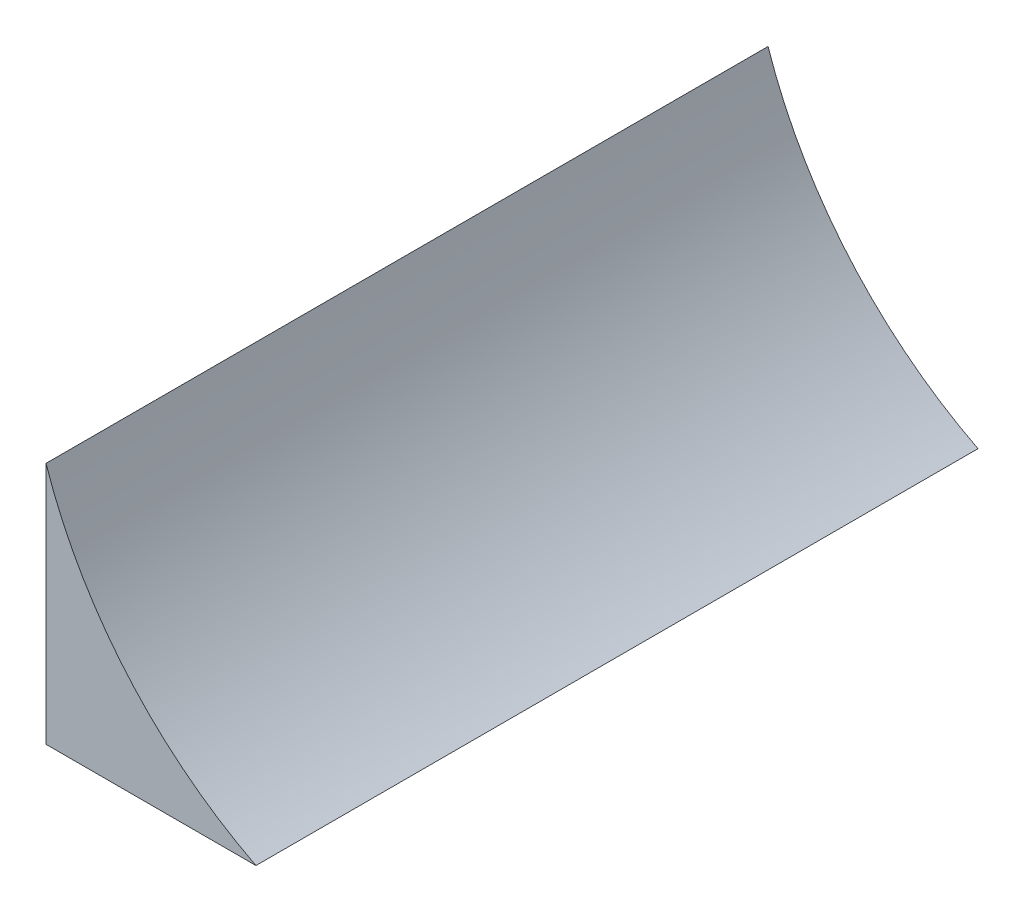
SolidWorks part; units mm, degrees
material "ASTM A36 Steel"
ref_plane "Front Plane" through (0, 0, 0) normal (0, 0, 1) x (1, 0, 0)
ref_plane "Top Plane" through (0, 0, 0) normal (0, 1, 0) x (1, 0, 0)
ref_plane "Right Plane" through (0, 0, 0) normal (1, 0, 0) x (0, 0, -1)
sketch "Sketch1" plane through (0, 0, 0) normal (0, 0, 1) x (1, 0, 0)
  line L0 (0, 0) -> (0, 85.6063)
  line L1 (0, 0) -> (73.8564, 0)
  arc A0 (73.8564, 0) -> (0, 85.6063) centre (141.9602, 133.419) cw
extrude "Boss-Extrude1" add sketch "Sketch1" along normal blind 254
